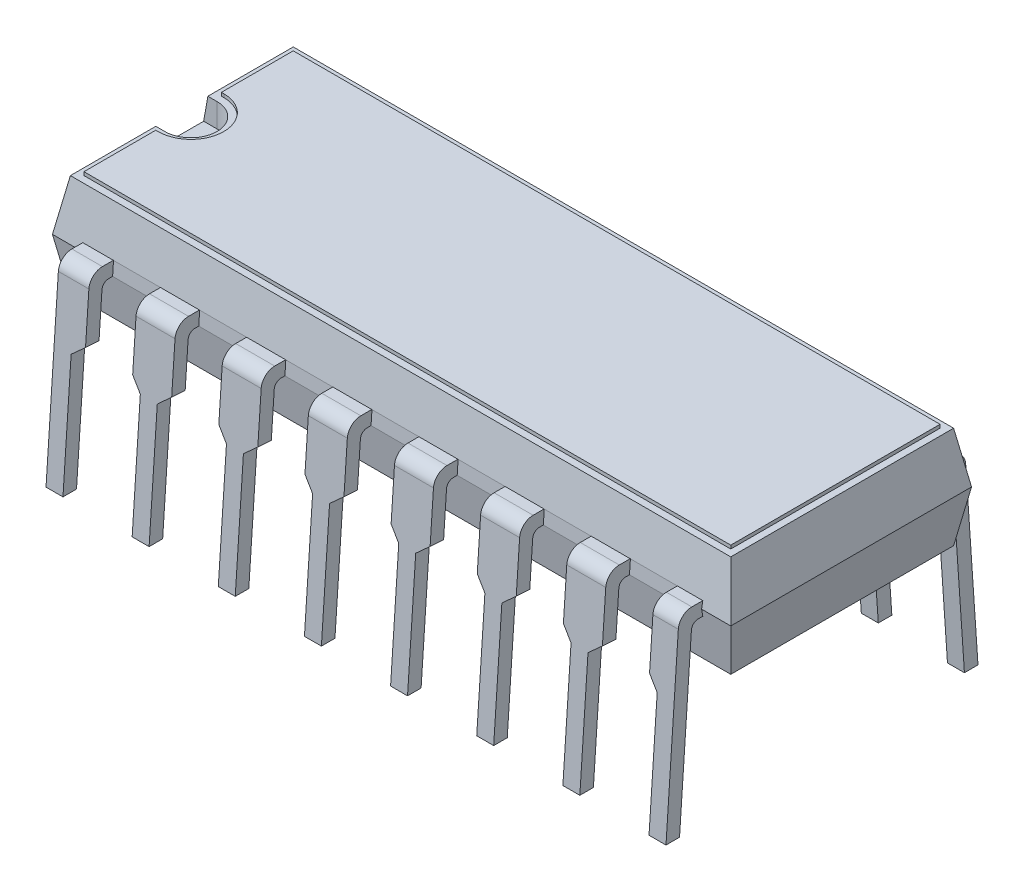
SolidWorks part; units mm, degrees
ref_plane "Front Plane" through (0, 0, 0) normal (0, 0, 1) x (1, 0, 0)
ref_plane "Top Plane" through (0, 0, 0) normal (0, 1, 0) x (1, 0, 0)
ref_plane "Right Plane" through (0, 0, 0) normal (1, 0, 0) x (0, 0, -1)
sketch "Sketch1" plane through (0, 0, 0) normal (0, 1, 0) x (1, 0, 0)
  line L1 (-10, 3.55) -> (10, 3.55)
  line L2 (-10, 3.55) -> (-10, -3.55)
  line L3 (-10, -3.55) -> (10, -3.55)
  line L4 (10, 3.55) -> (10, -3.55)
  line L5 (-10, 3.55) -> (10, -3.55) construction
  line L6 (-10, -3.55) -> (10, 3.55) construction
  point P0 (0, 0)
  dimension "D1" = 20
  dimension "D2" = 7.1
extrude "Boss-Extrude1" add sketch "Sketch1" along normal mid plane 3 draft 10
sketch "Sketch2" plane through (0, 1.5, 0) normal (0, 1, 0) x (1, 0, 0)
  line L0 (-10, 0) -> (-8.6988, 0) construction
  line L2 (-10, 3.55) -> (-10, -3.55) construction
  line L3 (-10, 0.7677) -> (-10, -0.7677)
  line L4 (-10, 0.7677) -> (-9.4665, 0.7677)
  line L5 (-10, -0.7677) -> (-9.4665, -0.7677)
  line L6 (-9.4665, 0.7677) -> (-9.4665, -0.7677) construction
  arc A0 (-9.4665, 0.7677) -> (-9.4665, -0.7677) centre (-9.4665, 0) cw
  point P9 (-10, 0)
  point P12 (-8.6988, 0)
extrude "Cut-Extrude1" cut sketch "Sketch2" against normal blind 0.7
sketch "Sketch4" plane through (0, 0, 0) normal (1, 0, 0) x (0, 0, -1)
  line L0 (0, 5.5) -> (0, -5.5) construction
  line L2 (-2.3444, 0.2) -> (-2.3444, -0.2)
  line L4 (-2.3444, -0.2) -> (-3.6508, -0.2)
  line L5 (4.4, -5.5) -> (-4.4, -5.5) construction
  line L6 (3.2855, -1.5) -> (-3.2855, -1.5) construction
  line L7 (-4.2, -5.5) -> (-4.6, -5.5)
  line L8 (3.55, 0) -> (-3.55, 0) construction
  line L9 (-2.3444, 0.2) -> (-3.8367, 0.2)
  line L10 (-4.2357, -0.1727) -> (-4.6, -5.5)
  line L11 (-3.8503, -0.3864) -> (-4.2, -5.5)
  arc A0 (-3.6508, -0.2) -> (-3.8503, -0.3864) centre (-3.6508, -0.4) ccw
  arc A1 (-3.8367, 0.2) -> (-4.2357, -0.1727) centre (-3.8367, -0.2) ccw
  point P6 (0, 0)
  point P9 (-2.3444, 0)
  point P11 (0, -5.5)
  point P16 (-4.4, -5.5)
  dimension "D4" = 0.4
  dimension "D5" = 0.2
  dimension "D1" = 0.4
  dimension "D2" = 4
  dimension "D3" = 8.8
extrude "Boss-Extrude2" add sketch "Sketch4" along normal mid plane 18.28
sketch "Sketch5" plane through (0, 0.2875, 4.2043) normal (0, 0.0682, 0.9977) x (1, 0, 0)
  line L0 (-8.64, -5.801) -> (-8.64, -2.2706)
  line L1 (9.14, -5.801) -> (-9.14, -5.801) construction
  line L2 (-8.64, -2.2706) -> (-8.24, -1.91)
  line L3 (-8.24, -1.91) -> (-8.24, -0.0402)
  line L4 (9.14, -0.0402) -> (-9.14, -0.0402) construction
  line L5 (-8.24, -0.0402) -> (-6.85, -0.0402)
  line L6 (-6.85, -0.0402) -> (-6.85, -1.91)
  line L7 (-6.85, -1.91) -> (-6.6, -2.2706)
  line L8 (-6.6, -2.2706) -> (-6.6, -5.801)
  line L9 (-9.14, -0.4613) -> (-9.14, -5.801) construction
  line L10 (-9.14, -5.801) -> (-8.64, -5.801) construction
  line L11 (-8.89, -5.801) -> (-8.89, -0.0402) construction
  line L12 (-6.6, -5.801) -> (-6.1, -5.801) construction
  line L13 (-6.35, -5.801) -> (-6.35, -0.0402) construction
  line L14 (-8.24, -1.91) -> (-6.85, -1.91) construction
  line L15 (-8.64, -2.2706) -> (-6.6, -2.2706) construction
  line L16 (-9.7355, -1.7206) -> (9.7355, -1.7206) construction
  line L17 (-8.89, -0.0402) -> (-8.24, -0.0402) construction
  line L18 (-6.85, -0.0402) -> (-6.35, -0.0402) construction
  line L19 (-8.64, -5.801) -> (-6.6, -5.801)
  line L20 (9.14, -5.801) -> (8.64, -5.801) construction
  line L21 (8.89, -5.801) -> (8.89, -0.0402) construction
  line L22 (-6.1, -5.801) -> (-6.1, -2.2706)
  line L23 (-6.1, -2.2706) -> (-5.7, -1.91)
  line L24 (-5.7, -1.91) -> (-5.7, -0.0402)
  line L25 (-5.7, -0.0402) -> (-4.31, -0.0402)
  line L26 (-4.31, -0.0402) -> (-4.31, -1.91)
  line L27 (-4.31, -1.91) -> (-4.06, -2.2706)
  line L28 (-4.06, -2.2706) -> (-4.06, -5.801)
  line L29 (-6.1, -5.801) -> (-4.06, -5.801)
  line L30 (-5.7, -1.91) -> (-4.31, -1.91) construction
  line L31 (-6.1, -2.2706) -> (-4.06, -2.2706) construction
  line L32 (-3.56, -5.801) -> (-3.56, -2.2706)
  line L33 (-3.56, -2.2706) -> (-3.16, -1.91)
  line L34 (-3.16, -1.91) -> (-3.16, -0.0402)
  line L35 (-3.16, -0.0402) -> (-1.77, -0.0402)
  line L36 (-1.77, -0.0402) -> (-1.77, -1.91)
  line L37 (-1.77, -1.91) -> (-1.52, -2.2706)
  line L38 (-1.52, -2.2706) -> (-1.52, -5.801)
  line L39 (-3.56, -5.801) -> (-1.52, -5.801)
  line L40 (-3.16, -1.91) -> (-1.77, -1.91) construction
  line L41 (-3.56, -2.2706) -> (-1.52, -2.2706) construction
  line L42 (-1.02, -5.801) -> (-1.02, -2.2706)
  line L43 (-1.02, -2.2706) -> (-0.62, -1.91)
  line L44 (-0.62, -1.91) -> (-0.62, -0.0402)
  line L45 (-0.62, -0.0402) -> (0.77, -0.0402)
  line L46 (0.77, -0.0402) -> (0.77, -1.91)
  line L47 (0.77, -1.91) -> (1.02, -2.2706)
  line L48 (1.02, -2.2706) -> (1.02, -5.801)
  line L49 (-1.02, -5.801) -> (1.02, -5.801)
  line L50 (-0.62, -1.91) -> (0.77, -1.91) construction
  line L51 (-1.02, -2.2706) -> (1.02, -2.2706) construction
  line L52 (1.52, -5.801) -> (1.52, -2.2706)
  line L53 (1.52, -2.2706) -> (1.92, -1.91)
  line L54 (1.92, -1.91) -> (1.92, -0.0402)
  line L55 (1.92, -0.0402) -> (3.31, -0.0402)
  line L56 (3.31, -0.0402) -> (3.31, -1.91)
  line L57 (3.31, -1.91) -> (3.56, -2.2706)
  line L58 (3.56, -2.2706) -> (3.56, -5.801)
  line L59 (1.52, -5.801) -> (3.56, -5.801)
  line L60 (1.92, -1.91) -> (3.31, -1.91) construction
  line L61 (1.52, -2.2706) -> (3.56, -2.2706) construction
  line L62 (4.06, -5.801) -> (4.06, -2.2706)
  line L63 (4.06, -2.2706) -> (4.46, -1.91)
  line L64 (4.46, -1.91) -> (4.46, -0.0402)
  line L65 (4.46, -0.0402) -> (5.85, -0.0402)
  line L66 (5.85, -0.0402) -> (5.85, -1.91)
  line L67 (5.85, -1.91) -> (6.1, -2.2706)
  line L68 (6.1, -2.2706) -> (6.1, -5.801)
  line L69 (4.06, -5.801) -> (6.1, -5.801)
  line L70 (4.46, -1.91) -> (5.85, -1.91) construction
  line L71 (4.06, -2.2706) -> (6.1, -2.2706) construction
  line L72 (6.6, -5.801) -> (6.6, -2.2706)
  line L73 (6.6, -2.2706) -> (7, -1.91)
  line L74 (7, -1.91) -> (7, -0.0402)
  line L75 (7, -0.0402) -> (8.39, -0.0402)
  line L76 (8.39, -0.0402) -> (8.39, -1.91)
  line L77 (8.39, -1.91) -> (8.64, -2.2706)
  line L78 (8.64, -2.2706) -> (8.64, -5.801)
  line L79 (6.6, -5.801) -> (8.64, -5.801)
  line L80 (7, -1.91) -> (8.39, -1.91) construction
  line L81 (6.6, -2.2706) -> (8.64, -2.2706) construction
  dimension "D1" = 0.5
  dimension "D2" = 0.9
  dimension "D3" = 0.5
  dimension "D4" = 2.54
  dimension "D5" = 1
  dimension "D6" = 0.55
  dimension "D7" = 0.5
  dimension "D8" = 7
extrude "Cut-Extrude2" cut sketch "Sketch5" against normal blind 0.7
mirror "Mirror1" about plane through (0, 0, 0) normal (0, 0, 1) of "Cut-Extrude2", "Boss-Extrude2"
sketch "Sketch6" plane through (0, 1.5, 0) normal (0, 1, 0) x (1, 0, 0)
  line L0 (-9.4665, 0.7677) -> (-9.7355, 0.7677) construction
  line L1 (9.7355, 3.2855) -> (-9.7355, 3.2855) construction
  line L2 (-9.7355, 3.2855) -> (-9.7355, 0.7677) construction
  line L4 (9.7355, -3.2855) -> (9.7355, 3.2855) construction
  line L5 (-9.7355, -3.2855) -> (9.7355, -3.2855) construction
  line L6 (-9.7355, -0.7677) -> (-9.7355, -3.2855) construction
  line L7 (-9.7355, -0.7677) -> (-9.4665, -0.7677) construction
  line L8 (9.7355, 3.2855) -> (-9.7355, 3.2855) construction
  line L9 (9.7355, -3.2855) -> (9.7355, 3.2855) construction
  line L10 (-9.7355, -3.2855) -> (9.7355, -3.2855) construction
  line L11 (-9.7355, -0.7677) -> (-9.7355, -3.2855) construction
  line L12 (-9.7355, -0.7677) -> (-9.4665, -0.7677) construction
  line L13 (-9.7355, 3.2855) -> (-9.7355, 0.7677) construction
  line L14 (-9.4665, 0.7677) -> (-9.7355, 0.7677) construction
  line L15 (9.5355, 3.0855) -> (-9.5355, 3.0855)
  line L16 (-9.5355, 3.0855) -> (-9.5355, 0.9677)
  line L17 (-9.4665, 0.9677) -> (-9.5355, 0.9677)
  line L18 (-9.5355, -0.9677) -> (-9.4665, -0.9677)
  line L19 (-9.5355, -0.9677) -> (-9.5355, -3.0855)
  line L20 (-9.5355, -3.0855) -> (9.5355, -3.0855)
  line L21 (9.5355, -3.0855) -> (9.5355, 3.0855)
  arc A0 (-9.4665, -0.7677) -> (-9.4665, 0.7677) centre (-9.4665, 0) ccw construction
  arc A1 (-9.4665, -0.7677) -> (-9.4665, 0.7677) centre (-9.4665, 0) ccw construction
  arc A2 (-9.4665, -0.9677) -> (-9.4665, 0.9677) centre (-9.4665, 0) ccw
  dimension "D1" = 0.2
extrude "Boss-Extrude3" add sketch "Sketch6" along normal blind 0.1
